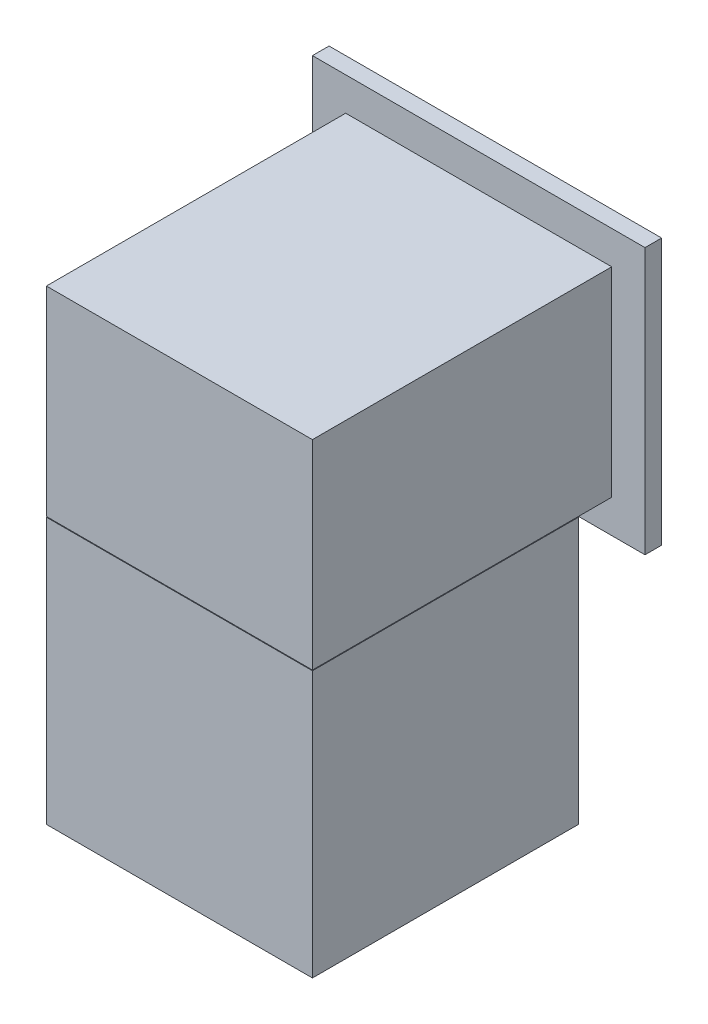
SolidWorks part; units mm, degrees
ref_plane "Front Plane" through (0, 0, 0) normal (0, 0, 1) x (1, 0, 0)
ref_plane "Top Plane" through (0, 0, 0) normal (0, 1, 0) x (1, 0, 0)
ref_plane "Right Plane" through (0, 0, 0) normal (1, 0, 0) x (0, 0, -1)
sketch "Sketch2" plane through (0, 0, 0) normal (1, 0, 0) x (0, 0, -1)
  line L0 (0, 600) -> (0, 700)
  line L1 (0, 0) -> (-900, 0)
  line L2 (0, 0) -> (0, -100)
  line L3 (0, 600) -> (-900, 600)
  line L4 (-900, 0) -> (-900, 600)
  line L5 (-100, -2) -> (-900, -2)
  line L6 (-100, -2) -> (-100, -802)
  line L7 (-100, -802) -> (-900, -802)
  line L8 (-900, -2) -> (-900, -802)
  line L9 (0, 700) -> (50, 700)
  line L10 (50, 300) -> (0, 300) construction
  line L11 (0, -100) -> (50, -100)
  line L12 (50, 700) -> (50, -100)
  line L13 (0, 460) -> (-26.9422, 460) construction
  line L14 (0, 460) -> (0, 140) construction
  line L15 (0, 140) -> (-26.9422, 140) construction
  line L16 (-26.9422, 460) -> (-26.9422, 140) construction
  line L17 (-26.9422, 300) -> (-900, 300) construction
  dimension "D1" = 320
  dimension "D2" = 50
  dimension "D3" = 100
  dimension "D4" = 800
  dimension "D5" = 800
  dimension "D6" = 100
  dimension "D7" = 2
  dimension "D8" = 800
extrude "Boss-Extrude1" add sketch "Sketch2" along normal blind 1000
sketch "Sketch3" plane through (0, 600, 0) normal (0, 1, 0) x (1, 0, 0)
  line L0 (1000, 0) -> (0, 0) construction
  line L1 (100, 0) -> (-222.974, 0)
  line L2 (100, 0) -> (100, -1016.5224)
  line L3 (100, -1016.5224) -> (-222.974, -1016.5224)
  line L4 (-222.974, 0) -> (-222.974, -1016.5224)
  line L5 (100, -1016.5224) -> (900, -1016.5224) construction
  line L6 (900, 0) -> (1310.4385, 0)
  line L7 (900, 0) -> (900, -1016.5224)
  line L8 (900, -1016.5224) -> (1310.4385, -1016.5224)
  line L9 (1310.4385, 0) -> (1310.4385, -1016.5224)
  line L10 (500, -1016.5224) -> (500, 0) construction
  line L11 (0, 0) -> (0, -900) construction
  dimension "D1" = 100
extrude "Cut-Extrude1" cut sketch "Sketch3" against normal blind 2189
sketch "Sketch4" plane through (0, 0, -50) normal (0, 0, -1) x (-1, 0, 0)
  line L0 (-1000, -100) -> (-1000, 700) construction
  line L1 (-900, 600) -> (-100, 600)
  line L2 (-900, 600) -> (-900, 0)
  line L3 (-900, 0) -> (-100, 0)
  line L4 (-100, 600) -> (-100, 0)
  line L5 (-1000, 700) -> (0, 700) construction
  line L6 (-100, 300) -> (0, 300) construction
  line L7 (0, -100) -> (0, 700) construction
  line L8 (-500, 0) -> (-500, -100) construction
  line L9 (-1000, -100) -> (0, -100) construction
  dimension "D1" = 100
  dimension "D2" = 100
extrude "Cut-Extrude2" cut sketch "Sketch4" against normal blind 10
sketch "Sketch5" plane through (0, 0, -40) normal (0, 0, -1) x (-1, 0, 0)
  line L0 (-100, 600) -> (-900, 600) construction
  line L1 (-870, 570) -> (-280, 570)
  line L2 (-870, 570) -> (-870, 30)
  line L3 (-870, 30) -> (-280, 30)
  line L4 (-280, 570) -> (-280, 30)
  line L5 (-900, 600) -> (-900, 0) construction
  line L6 (-870, 300) -> (-900, 300) construction
  line L7 (-900, 600) -> (-900, 0) construction
  line L8 (-100, 0) -> (-100, 600) construction
  dimension "D1" = 30
  dimension "D2" = 30
  dimension "D3" = 180
extrude "Cut-Extrude3" cut sketch "Sketch5" against normal blind 200 draft 15
sketch "Sketch6" plane through (0, 0, 160) normal (0, 0, -1) x (-1, 0, 0)
  line L0 (-575, 476.4102) -> (-575, 516.4102) construction
  line L1 (-405, 476.4102) -> (-745, 476.4102)
  line L2 (-405, 476.4102) -> (-405, 206.4102)
  line L3 (-405, 206.4102) -> (-745, 206.4102)
  line L4 (-745, 476.4102) -> (-745, 206.4102)
  line L5 (-333.5898, 516.4102) -> (-816.4102, 516.4102) construction
  line L8 (-775.3285, 516.4102) -> (-775.3285, 146.4102) construction
  line L10 (-783.5898, 95) -> (-583.5898, 95)
  line L11 (-563.5898, 135) -> (-363.5898, 135)
  line L12 (-563.5898, 135) -> (-563.5898, 95)
  line L13 (-563.5898, 95) -> (-363.5898, 95)
  line L14 (-363.5898, 135) -> (-363.5898, 95)
  line L15 (-775.3285, 146.4102) -> (-775.3285, 83.5898) construction
  line L16 (-816.4102, 83.5898) -> (-333.5898, 83.5898) construction
  line L17 (-775.3285, 115) -> (-563.5898, 115) construction
  line L18 (-583.5898, 135) -> (-583.5898, 95)
  line L19 (-783.5898, 135) -> (-583.5898, 135)
  line L20 (-783.5898, 135) -> (-783.5898, 95)
  line L21 (-563.5898, 95) -> (-783.5898, 95) construction
  line L22 (-333.5898, 83.5898) -> (-333.5898, 516.4102) construction
  circle A0 centre (-575, 496.4102) radius 5
  dimension "D10" = 10
  dimension "D1" = 340
  dimension "D2" = 270
  dimension "D3" = 370
  dimension "D4" = 40
  dimension "D5" = 200
  dimension "D6" = 40
  dimension "D8" = 220
  dimension "D9" = 30
  dimension "D7" = 2
extrude "Cut-Extrude4" cut sketch "Sketch6" against normal blind 10
